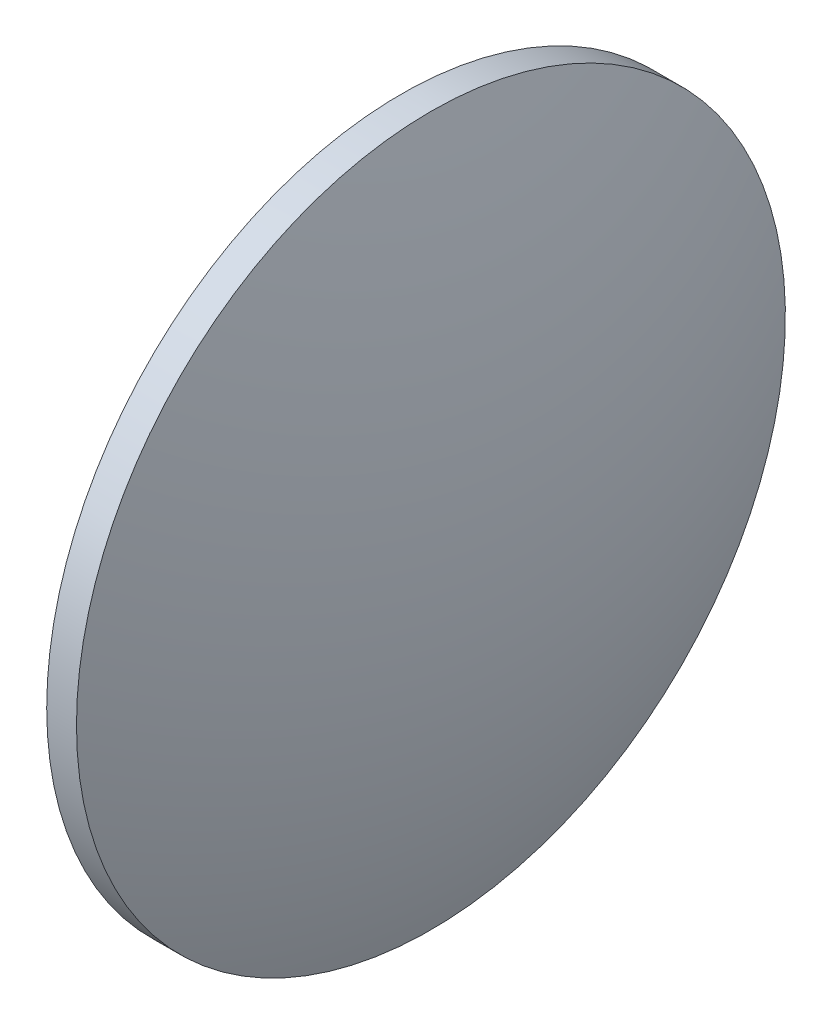
SolidWorks part; units mm, degrees
ref_plane "前视基准面" through (0, 0, 0) normal (0, 0, 1) x (1, 0, 0)
ref_plane "上视基准面" through (0, 0, 0) normal (0, 1, 0) x (1, 0, 0)
ref_plane "右视基准面" through (0, 0, 0) normal (1, 0, 0) x (0, 0, -1)
sketch "草图1" plane through (0, 0, 0) normal (0, 0, 1) x (1, 0, 0)
  line L0 (434.0287, 60.4635) -> (460.9202, 60.4635) construction
  line L1 (443.4635, 60.4635) -> (443.4635, 82.9635)
  line L2 (449.5635, 60.4635) -> (443.4635, 60.4635)
  line L5 (443.4635, 82.9635) -> (445.3535, 82.9635)
  arc A0 (449.5635, 60.4635) -> (445.3535, 82.9635) centre (387.3338, 60.4635) ccw
revolve "旋转1" add sketch "草图1" angle 360 about L0
